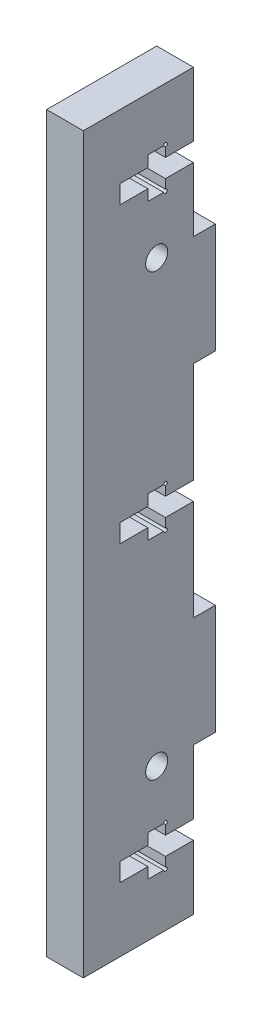
SolidWorks part; units mm, degrees
material "PMMA"
ref_plane "Front Plane" through (0, 0, 0) normal (0, 0, 1) x (1, 0, 0)
ref_plane "Top Plane" through (0, 0, 0) normal (0, 1, 0) x (1, 0, 0)
ref_plane "Right Plane" through (0, 0, 0) normal (1, 0, 0) x (0, 0, -1)
sketch "Schizzo1" plane through (0, 0, 0) normal (1, 0, 0) x (0, 0, -1)
  line L0 (-7.5, 50) -> (7.5, -50) construction
  line L1 (-7.5, 50) -> (7.5, 50)
  line L2 (-7.5, 50) -> (-7.5, -50)
  line L3 (-7.5, -50) -> (7.5, -50)
  line L4 (7.5, 50) -> (7.5, -50)
  point P4 (0, 0)
  dimension "D1" = 100
  dimension "D2" = 15
extrude "Estrusione-Estrusione1" add sketch "Schizzo1" along normal blind 5
sketch "Schizzo2" plane through (0, 0, -7.5) normal (0, 0, -1) x (-1, 0, 0)
  line L0 (-5, 0) -> (0, 0) construction
  line L1 (-5, 30) -> (0, 30)
  line L2 (-5, 30) -> (-5, 15)
  line L3 (-5, 15) -> (0, 15)
  line L4 (0, 30) -> (0, 15)
  line L5 (-5, -50) -> (-5, 50) construction
  line L7 (0, -50) -> (0, 50) construction
  line L8 (-5, -30) -> (-5, -15)
  line L9 (-5, -15) -> (0, -15)
  line L10 (0, -30) -> (0, -15)
  line L11 (-5, -30) -> (0, -30)
  dimension "D1" = 15
  dimension "D2" = 15
extrude "Estrusione-Estrusione2" add sketch "Schizzo2" along normal blind 3
sketch "Schizzo4" plane through (0, 0, 0) normal (1, 0, 0) x (0, 0, -1)
  line L0 (2.5, 50) -> (2.5, -50) construction
  line L1 (7.5, 50) -> (-7.5, 50) construction
  line L2 (-7.5, -50) -> (7.5, -50) construction
  line L3 (7.5, 30) -> (7.5, 50) construction
  line L4 (7.5, 0) -> (-7.5, 0) construction
  line L5 (7.5, -15) -> (7.5, 15) construction
  line L6 (-7.5, 50) -> (-7.5, -50) construction
  line L7 (7.5, 30) -> (7.5, 50) construction
  circle A1 centre (2.5, 30) radius 1.5
  circle A2 centre (2.5, -30) radius 1.5
  dimension "D3" = 20
  dimension "D1" = 5
extrude "Taglio-Estrusione2" cut sketch "Schizzo4" along direction (1, 0, 0) on the side of the normal through all
sketch "Schizzo5" plane through (5, 0, 0) normal (1, 0, 0) x (0, 0, -1)
  line L0 (-8.3871, 0) -> (1.6129, 0) construction
  line L1 (-2.5, 1.25) -> (1.3, 1.25)
  line L2 (1.3, 1.25) -> (1.3, 2.75)
  line L3 (1.3, 2.75) -> (3.7, 2.75)
  line L4 (3.7, 2.75) -> (3.7, 1.25)
  line L5 (3.7, 1.25) -> (7.5, 1.25)
  line L6 (7.5, 1.25) -> (7.5, -1.25)
  line L7 (7.5, -1.25) -> (3.7, -1.25)
  line L8 (3.7, -1.25) -> (3.7, -2.75)
  line L9 (3.7, -2.75) -> (1.3, -2.75)
  line L10 (1.3, -2.75) -> (1.3, -1.25)
  line L11 (1.3, -1.25) -> (-2.5, -1.25)
  line L12 (-2.5, -1.25) -> (-2.5, 1.25)
  line L13 (7.5, 0) -> (-7.5, 0) construction
  line L14 (7.5, -15) -> (7.5, 15) construction
  line L15 (-7.5, 50) -> (-7.5, -50) construction
  line L16 (-2.5, -38.75) -> (1.3, -38.75)
  line L17 (1.3, -38.75) -> (1.3, -37.25)
  line L18 (1.3, -37.25) -> (3.7, -37.25)
  line L19 (3.7, -37.25) -> (3.7, -38.75)
  line L20 (3.7, -38.75) -> (7.5, -38.75)
  line L21 (7.5, -38.75) -> (7.5, -41.25)
  line L22 (7.5, -41.25) -> (3.7, -41.25)
  line L23 (3.7, -41.25) -> (3.7, -42.75)
  line L24 (3.7, -42.75) -> (1.3, -42.75)
  line L25 (1.3, -42.75) -> (1.3, -41.25)
  line L26 (1.3, -41.25) -> (-2.5, -41.25)
  line L27 (-2.5, -41.25) -> (-2.5, -38.75)
  line L28 (7.5, 38.75) -> (7.5, 41.25)
  line L29 (3.7, 38.75) -> (7.5, 38.75)
  line L30 (3.7, 37.25) -> (3.7, 38.75)
  line L31 (1.3, 37.25) -> (3.7, 37.25)
  line L32 (1.3, 38.75) -> (1.3, 37.25)
  line L33 (-2.5, 38.75) -> (1.3, 38.75)
  line L34 (-2.5, 41.25) -> (-2.5, 38.75)
  line L35 (1.3, 41.25) -> (-2.5, 41.25)
  line L36 (1.3, 42.75) -> (1.3, 41.25)
  line L37 (3.7, 42.75) -> (1.3, 42.75)
  line L38 (3.7, 41.25) -> (3.7, 42.75)
  line L39 (7.5, 41.25) -> (3.7, 41.25)
  dimension "D1" = 5.5
  dimension "D2" = 2.5
  dimension "D3" = 1.25
  dimension "D4" = 2.75
  dimension "D5" = 2.4
  dimension "D6" = 10
  dimension "D7" = 2
  dimension "D8" = 1
extrude "Taglio-Estrusione3" cut sketch "Schizzo5" along direction (1, 0, 0) on the side against the normal through all
sketch "Schizzo6" plane through (5, 0, 0) normal (1, 0, 0) x (0, 0, -1)
  circle A0 centre (3.7, 42.75) radius 0.25
  circle A1 centre (3.7, 37.25) radius 0.25
  circle A3 centre (3.7, 2.75) radius 0.25
  circle A4 centre (3.7, -2.75) radius 0.25
  circle A5 centre (3.7, -37.25) radius 0.25
  circle A6 centre (3.7, -42.75) radius 0.25
  dimension "D1" = 0.5
  dimension "D2" = 0.5
  dimension "D3" = 0.5
extrude "Taglio-Estrusione4" cut sketch "Schizzo6" against normal blind 10
equation "\"Thickness5\"=5"
equation "\"D1@Estrusione-Estrusione1\"=\"Thickness5\""
equation "\"Thickness3\"=3"
equation "\"D1@Estrusione-Estrusione2\"=\"Thickness3\""
